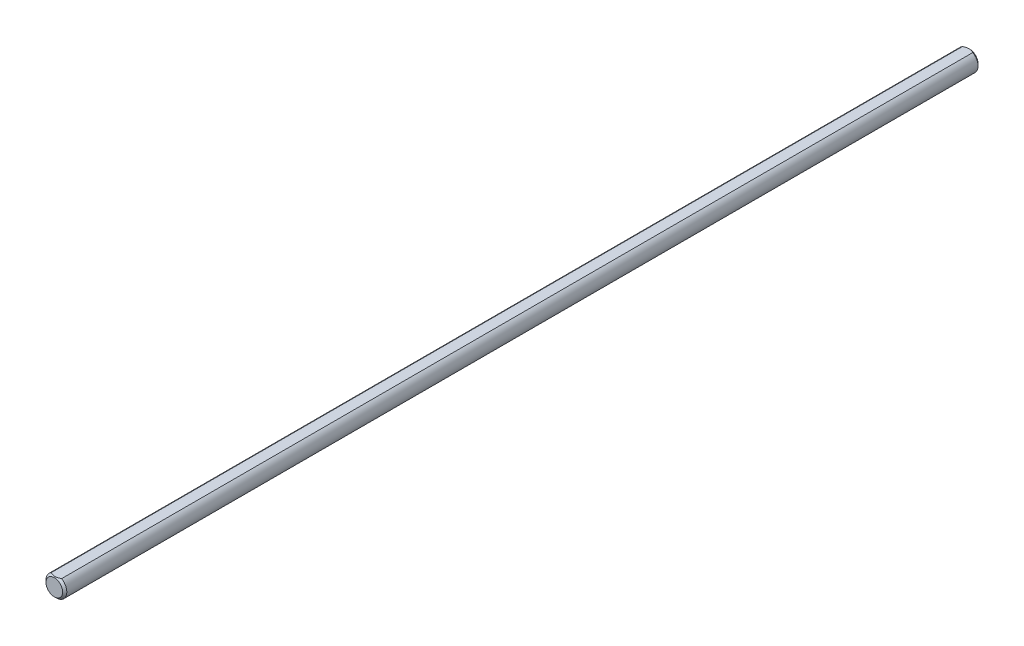
SolidWorks part; units mm, degrees
ref_plane "Front" through (0, 0, 0) normal (0, 0, 1) x (1, 0, 0)
ref_plane "Top" through (0, 0, 0) normal (0, 1, 0) x (1, 0, 0)
ref_plane "Right" through (0, 0, 0) normal (1, 0, 0) x (0, 0, -1)
sketch "Sketch1" plane through (0, 0, 0) normal (0, 0, 1) x (1, 0, 0)
  circle A0 centre (0, 0) radius 3.175
  dimension "D1" = 6.35
extrude "Extrude1" add sketch "Sketch1" along normal mid plane 279.4
chamfer "Chamfer1" distance 0.635 angle 45 2 edges at (3.175, 0, -139.7) (3.175, 0, 139.7)
sketch "Sketch13" plane through (0, 0, 0) normal (0, 0, 1) x (1, 0, 0)
  line L3 (-1.5875, 2.7496) -> (1.5875, 2.7496)
  circle A0 centre (0, 0) radius 3.175 construction
  arc A1 (1.5875, 2.7496) -> (-1.5875, 2.7496) centre (0, 0) ccw
  dimension "D1" = 3.175
extrude "Extrude7" cut sketch "Sketch13" against normal through all and the other way through all
equation "\"D1@Chamfer1\" = \"D1@Sketch1\" * .1"
equation "\"D1@Sketch13\" = \"D1@Sketch1\" * .5"
